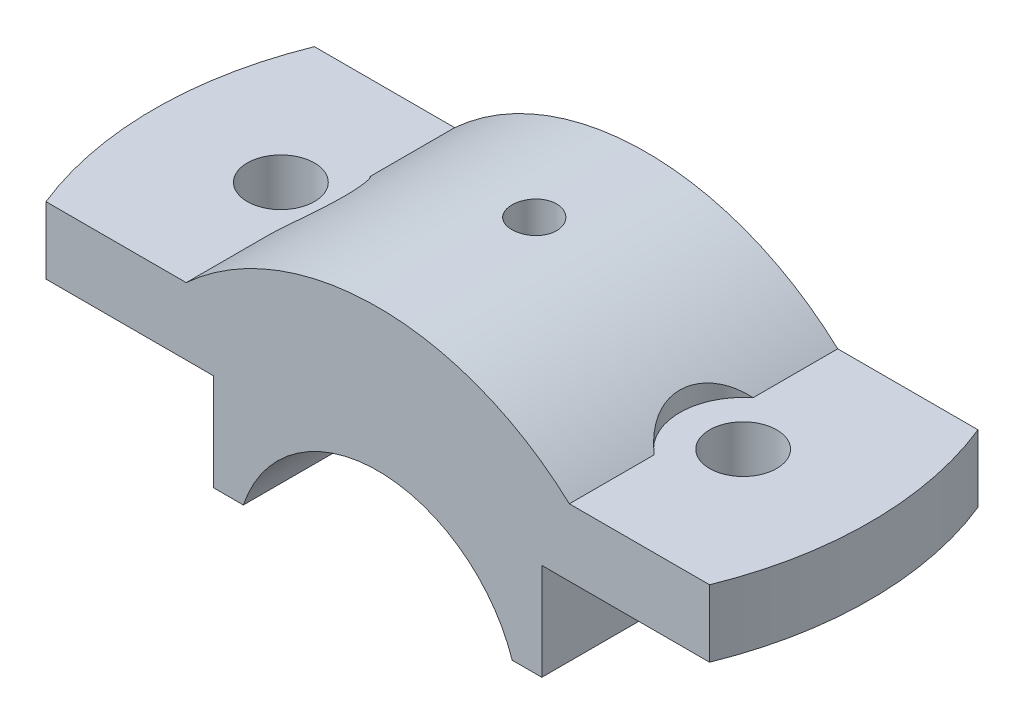
SolidWorks part; units mm, degrees
material "Malleable Cast Iron"
ref_plane "Front" through (0, 0, 0) normal (0, 0, 1) x (1, 0, 0)
ref_plane "Top" through (0, 0, 0) normal (0, 1, 0) x (1, 0, 0)
ref_plane "Right" through (0, 0, 0) normal (1, 0, 0) x (0, 0, -1)
sketch "Sketch1" plane through (0, 0, 0) normal (0, 0, 1) x (1, 0, 0)
  line L0 (0, 0) -> (0, 46.6461) construction
  line L1 (18.0278, 6) -> (22, 6)
  line L2 (22, 6) -> (22, 19)
  line L3 (22, 19) -> (50, 19)
  line L4 (50, 19) -> (50, 28)
  line L5 (50, 28) -> (25.6905, 28)
  line L6 (-18.0278, 6) -> (-22, 6)
  line L7 (-22, 6) -> (-22, 19)
  line L8 (-22, 19) -> (-50, 19)
  line L9 (-50, 19) -> (-50, 28)
  line L10 (-50, 28) -> (-25.6905, 28)
  arc A0 (25.6905, 28) -> (-25.6905, 28) centre (0, 0) ccw
  arc A1 (18.0278, 6) -> (-18.0278, 6) centre (0, 0) ccw
  dimension "D1" = 19
  dimension "D2" = 38
  dimension "D3" = 6
  dimension "D4" = 13
  dimension "D5" = 44
  dimension "D6" = 9
  dimension "D7" = 50
extrude "Boss-Extrude1" add sketch "Sketch1" along normal mid plane 36
sketch "Sketch3" plane through (0, 28, 0) normal (0, 1, 0) x (1, 0, 0)
  line L0 (-25.6905, 18) -> (-50, 18) construction
  line L1 (-50, -18) -> (-50, 18) construction
  line L2 (-25.6905, -18) -> (-50, -18) construction
  line L3 (-44.4972, 18) -> (-50, 18)
  line L4 (-50, -18) -> (-50, 18)
  line L5 (-44.4972, -18) -> (-50, -18)
  arc A0 (-44.4972, 18) -> (-44.4972, -18) centre (0, 0) ccw
  dimension "D1" = 48
extrude "Cut-Extrude1" cut sketch "Sketch3" against normal through all
hole_wizard "Ø12.0mm Dowel Hole3" positions "Sketch15" profile "Sketch14" hole size "Ø12.0" standard "ANSI Metric" end condition through all
sketch "Sketch15" plane through (0, 28, 0) normal (0, 1, 0) x (1, 0, 0)
  point P0 (-31, 0)
  dimension "D1" = 31
sketch "Sketch14" plane through (-31, 28, 0) normal (1, 0, 0) x (0, 0, 1)
  line L0 (0, 0) -> (0, 22)
  line L1 (0, 22) -> (4.5, 22)
  line L2 (4.5, 22) -> (4.5, 0)
  line L5 (4.5, 0) -> (0, 0)
  line L11 (0, -6.35) -> (0, 107.95) construction
  dimension "Thru Hole Dia." = 9
  dimension "Thru Hole Depth" = 22
sketch "Sketch17" plane through (0, 28, 0) normal (0, 1, 0) x (1, 0, 0)
  line L0 (-25.6905, -18) -> (-25.6905, 18) construction
  line L1 (-25.6905, -6.6377) -> (-25.6905, 6.6377)
  arc A0 (-25.6905, -6.6377) -> (-25.6905, 6.6377) centre (-31, 0) ccw
  dimension "D1" = 8.5
extrude "Cut-Extrude5" cut sketch "Sketch17" along normal blind 36
hole_wizard "CBORE for M6 Hex Head Bolt1" positions "3DSketch2" profile "Sketch20" counterbore size "M6" standard "ANSI Metric" end condition through all
sketch3d "3DSketch2"
  point P0 (0, 38, -2.9839)
  dimension "D1" = 0
sketch "Sketch20" plane through (0, 38, -2.9839) normal (1, 0, 0) x (0, 0, 1)
  line L0 (0, 0) -> (0, 32)
  line L1 (0, 32) -> (2.5, 32)
  line L2 (2.5, 13.495) -> (2.5, 32)
  line L3 (2.5, 13.495) -> (2.995, 13)
  line L4 (2.995, 13) -> (3, 13)
  line L5 (3, 13) -> (3, 0)
  line L7 (0, 0) -> (3, 0)
  line L9 (-2.5, 13.495) -> (-2.995, 13) construction
  line L11 (0, -6.35) -> (0, 107.95) construction
  dimension "Thru Hole Dia." = 5
  dimension "Thru Hole Depth" = 32
  dimension "C'Bore Dia." = 6
  dimension "C'Bore Depth" = 13
  dimension "Mid C'Sink Dia." = 5.99
  dimension "Mid C'Sink Angle" = 90
mirror "Mirror1" about plane through (0, 0, 0) normal (1, 0, 0) of "Cut-Extrude1", "Ø12.0mm Dowel Hole3", "Cut-Extrude5"
